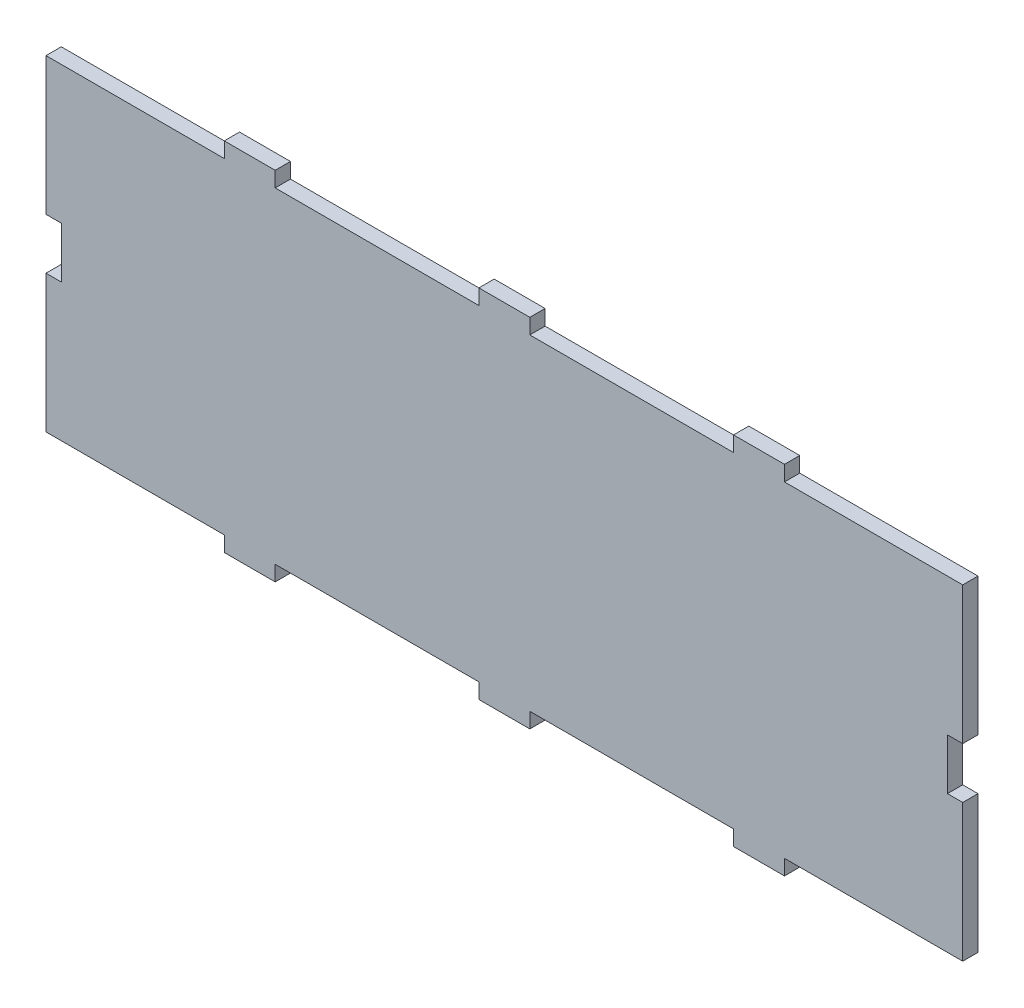
SolidWorks part; units mm, degrees
ref_plane "Front Plane" through (0, 0, 0) normal (0, 0, 1) x (1, 0, 0)
ref_plane "Top Plane" through (0, 0, 0) normal (0, 1, 0) x (1, 0, 0)
ref_plane "Right Plane" through (0, 0, 0) normal (1, 0, 0) x (0, 0, -1)
sketch "Sketch3" plane through (0, 0, 0) normal (0, 0, 1) x (1, 0, 0)
  line L1 (-90, -35) -> (90, -35)
  line L2 (-90, -35) -> (-90, 35)
  line L3 (-90, 35) -> (90, 35)
  line L4 (90, -35) -> (90, 35)
  line L5 (-90, -35) -> (90, 35) construction
  line L6 (-90, 35) -> (90, -35) construction
  point P0 (0, 0)
  dimension "D1" = 180
  dimension "D2" = 70
extrude "Boss-Extrude1" add sketch "Sketch3" along normal blind 3
sketch "Sketch4" plane through (0, 0, 3) normal (0, 0, 1) x (1, 0, 0)
  line L0 (0, 0) -> (0, 35) construction
  line L1 (90, 35) -> (-90, 35) construction
  line L2 (0, 35) -> (0, -35) construction
  line L3 (-90, -35) -> (90, -35) construction
  line L4 (0, -35) -> (0, 0) construction
  line L5 (0, 0) -> (90, 0) construction
  line L6 (90, -35) -> (90, 35) construction
  line L7 (90, 0) -> (0, 0) construction
  line L8 (0, 0) -> (-90, 0) construction
  line L9 (-90, 35) -> (-90, -35) construction
  line L10 (-5, -35) -> (-45, -35)
  line L11 (0, -35) -> (-5, -35)
  line L12 (0, -35) -> (0, -32)
  line L13 (0, -32) -> (-5, -32)
  line L14 (-5, -35) -> (-5, -32)
  line L15 (0, -35) -> (5, -35)
  line L16 (0, -35) -> (0, -32)
  line L17 (0, -32) -> (5, -32)
  line L18 (5, -35) -> (5, -32)
  line L20 (5, -35) -> (5, -32)
  line L22 (90, -35) -> (90, -32)
  line L23 (-5, -35) -> (-90, -35)
  line L24 (-5, -35) -> (-5, -32)
  line L26 (-90, -35) -> (-90, -32)
  line L27 (5, -35) -> (45, -35)
  line L28 (-45, -35) -> (-55, -35)
  line L29 (-45, -35) -> (-45, -32)
  line L30 (-45, -32) -> (-55, -32)
  line L31 (-55, -35) -> (-55, -32)
  line L32 (5, -35) -> (45, -35)
  line L34 (45, -35) -> (55, -35)
  line L35 (45, -35) -> (45, -32)
  line L36 (45, -32) -> (55, -32)
  line L37 (55, -35) -> (55, -32)
  line L38 (0, 35) -> (5, 35)
  line L39 (0, 35) -> (0, 32)
  line L40 (0, 32) -> (5, 32)
  line L41 (5, 35) -> (5, 32)
  line L42 (0, 35) -> (-5, 35)
  line L43 (0, 35) -> (0, 32)
  line L44 (0, 32) -> (-5, 32)
  line L45 (-5, 35) -> (-5, 32)
  line L46 (45, 35) -> (55, 35)
  line L47 (45, 35) -> (45, 32)
  line L48 (45, 32) -> (55, 32)
  line L49 (55, 35) -> (55, 32)
  line L50 (-45, 35) -> (-55, 35)
  line L51 (-45, 35) -> (-45, 32)
  line L52 (-45, 32) -> (-55, 32)
  line L53 (-55, 35) -> (-55, 32)
  line L56 (-90, 5) -> (-87, 5)
  line L60 (-90, -5) -> (-87, -5)
  line L61 (-87, 0) -> (-87, -5)
  line L62 (90, 0) -> (87, 0)
  line L63 (90, 0) -> (90, 5)
  line L64 (90, 5) -> (87, 5)
  line L65 (87, 0) -> (87, 5)
  line L66 (90, 0) -> (87, 0)
  line L67 (90, 0) -> (90, -5)
  line L68 (90, -5) -> (87, -5)
  line L69 (87, 0) -> (87, -5)
  line L70 (-5, 35) -> (-45, 35)
  line L71 (-5, 35) -> (-5, 32)
  line L72 (-5, 32) -> (-45, 32)
  line L73 (-45, 35) -> (-45, 32)
  line L74 (-55, 35) -> (-90, 35)
  line L75 (-55, 35) -> (-55, 32)
  line L76 (-55, 32) -> (-90, 32)
  line L77 (-90, 35) -> (-90, 32)
  line L78 (5, 35) -> (45, 35)
  line L79 (5, 35) -> (5, 32)
  line L80 (5, 32) -> (45, 32)
  line L81 (45, 35) -> (45, 32)
  line L82 (55, 35) -> (90, 35)
  line L83 (55, 35) -> (55, 32)
  line L84 (55, 32) -> (90, 32)
  line L85 (90, 35) -> (90, 32)
  line L86 (-55, -32) -> (-90, -32)
  line L87 (-55, -32) -> (-55, -35)
  line L88 (-55, -35) -> (-90, -35)
  line L89 (-90, -32) -> (-90, -35)
  line L90 (-45, -35) -> (-5, -35)
  line L91 (-45, -35) -> (-45, -32)
  line L92 (-45, -32) -> (-5, -32)
  line L93 (-5, -35) -> (-5, -32)
  line L94 (5, -35) -> (45, -35)
  line L95 (5, -35) -> (5, -32)
  line L96 (5, -32) -> (45, -32)
  line L97 (45, -35) -> (45, -32)
  line L98 (55, -35) -> (90, -35)
  line L99 (55, -35) -> (55, -32)
  line L100 (55, -32) -> (90, -32)
  line L101 (90, -35) -> (90, -32)
  line M4 (90, -35) -> (90, 35)
  line M5 (90, 35) -> (-90, 35)
  line M6 (-90, 35) -> (-90, -35)
  line M7 (-90, -35) -> (90, -35)
  dimension "D1" = 3
  dimension "D2" = 5
  dimension "D3" = 5
  dimension "D4" = 40
  dimension "D5" = 10
  dimension "D6" = 40
  dimension "D7" = 10
  dimension "D8" = 3
  dimension "D9" = 5
  dimension "D10" = 3
  dimension "D11" = 5
  dimension "D12" = 3
sketch "Sketch5" plane through (0, 0, 3) normal (0, 0, 1) x (1, 0, 0)
  line L0 (0, 0) -> (0, -35)
  line L1 (-90, -35) -> (90, -35) construction
  line L2 (0, -35) -> (0, 0)
  line L3 (0, 0) -> (0, 35)
  line L4 (90, 35) -> (-90, 35) construction
  line L5 (0, 35) -> (0, 0)
  line L6 (90, 0) -> (0, 0)
  line L7 (90, -35) -> (90, 35) construction
  line L8 (-90, 0) -> (0, 0)
  line L9 (-90, 35) -> (-90, -35) construction
  line L11 (90, 0) -> (87, 0)
  line L12 (90, 0) -> (90, 5)
  line L13 (90, 5) -> (87, 5)
  line L14 (87, 0) -> (87, 5)
  line L16 (90, 0) -> (87, 0)
  line L17 (90, 0) -> (90, -5)
  line L18 (90, -5) -> (87, -5)
  line L19 (87, 0) -> (87, -5)
  line L20 (-90, 0) -> (-87, 0)
  line L21 (-90, 0) -> (-90, 5)
  line L22 (-90, 5) -> (-87, 5)
  line L23 (-87, 0) -> (-87, 5)
  line L24 (-90, 0) -> (-87, 0)
  line L25 (-90, 0) -> (-90, -5)
  line L26 (-90, -5) -> (-87, -5)
  line L27 (-87, 0) -> (-87, -5)
  line M11 (90, -35) -> (90, 35)
  line M13 (-90, 35) -> (-90, -35)
  dimension "D1" = 3
  dimension "D2" = 5
  dimension "D3" = 5
  dimension "D4" = 5
  dimension "D5" = 5
  dimension "D6" = 3
extrude "Cut-Extrude2" cut sketch "Sketch5" against normal blind 3 contours L8 L23 L22 M13 | L27 L8 L26 M13 | L14 L6 L13 M11 | L6 L19 L18 M11
extrude "Cut-Extrude3" cut sketch "Sketch4" against normal blind 10 contours L76 L53 M5 M6 | L72 L45 L51 M5 | L41 L80 L47 M5 | L49 L84 M4 M5 | L100 L37 M7 M4 | L96 L18 L35 M7 | L92 L29 L14 M7 | L31 L86 M6 M7
